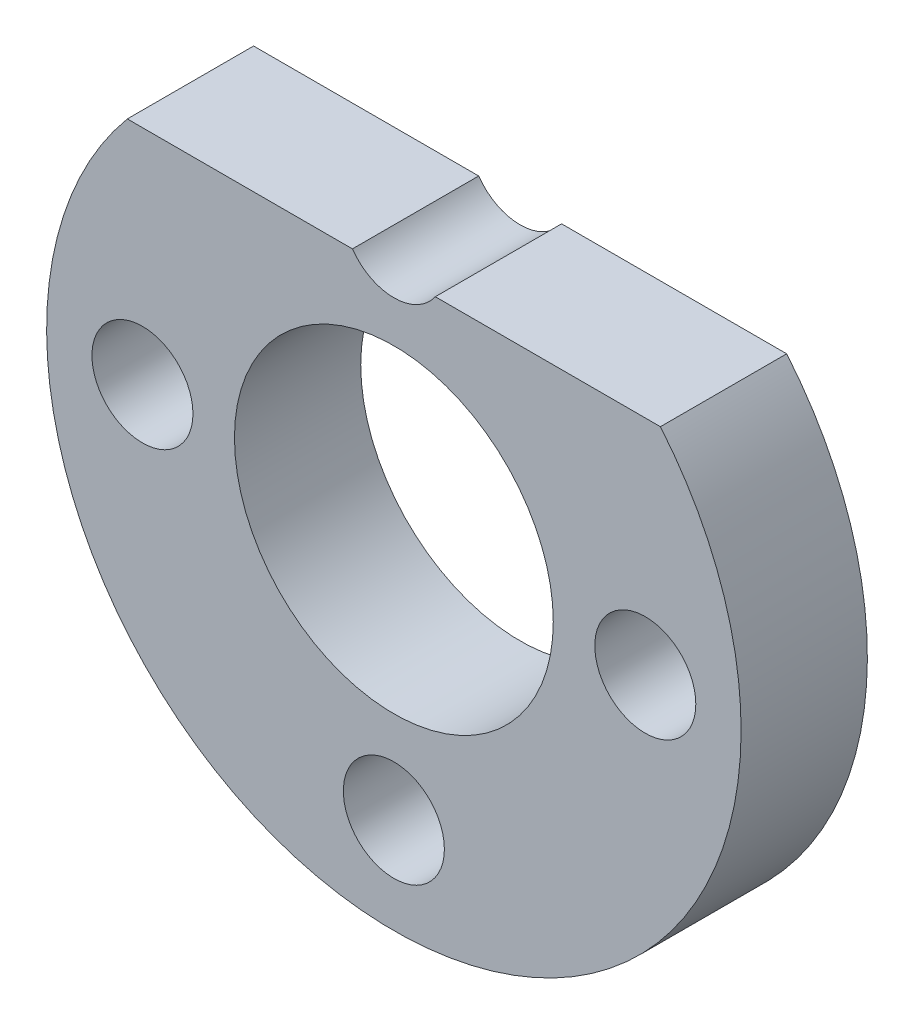
SolidWorks part; units mm, degrees
material "Thornel Mat VMA"
ref_plane "Plano frontal" through (0, 0, 0) normal (0, 0, 1) x (1, 0, 0)
ref_plane "Plano superior" through (0, 0, 0) normal (0, 1, 0) x (1, 0, 0)
ref_plane "Plano direito" through (0, 0, 0) normal (1, 0, 0) x (0, 0, -1)
sketch "Esboço1" plane through (0, 0, 0) normal (0, 0, 1) x (1, 0, 0)
  line L0 (95.2028, -295.7159) -> (112.0904, -295.7159)
  circle A0 centre (103.6466, -302.7659) radius 7.9647 construction
  arc A1 (95.2028, -295.7159) -> (112.0904, -295.7159) centre (103.6466, -302.7659) ccw
  dimension "D1" = 11
extrude "Ressalto-extrusão1" add sketch "Esboço1" along normal blind 4
sketch "Esboço2" plane through (0, 0, 4) normal (0, 0, 1) x (1, 0, 0)
  circle A0 centre (103.6466, -302.7659) radius 5.05
  dimension "D1" = 10.1
extrude "Corte-extrusão1" cut sketch "Esboço2" against normal blind 4
hole_wizard "M3 Clearance Hole1" positions "Sketch3" profile "Sketch2" hole size "M3" standard "ISO" end condition through all
sketch "Sketch3" plane through (0, 0, 4) normal (0, 0, 1) x (1, 0, 0)
  circle A0 centre (103.6466, -302.7659) radius 7.9647
  point P4 (95.6819, -302.7659)
  point P6 (111.6113, -302.7659)
  point P8 (103.6466, -310.7307)
  point P10 (103.6466, -294.8012)
sketch "Sketch2" plane through (95.6819, -302.7659, 4) normal (1, 0, 0) x (0, -1, 0)
  line L0 (0, 0) -> (0, 4)
  line L1 (0, 4) -> (1.6, 4)
  line L2 (1.6, 4) -> (1.6, 0)
  line L5 (1.6, 0) -> (0, 0)
  line L11 (0, -6.35) -> (0, 107.95) construction
  dimension "Thru Hole Dia." = 3.2
  dimension "Thru Hole Depth" = 4
